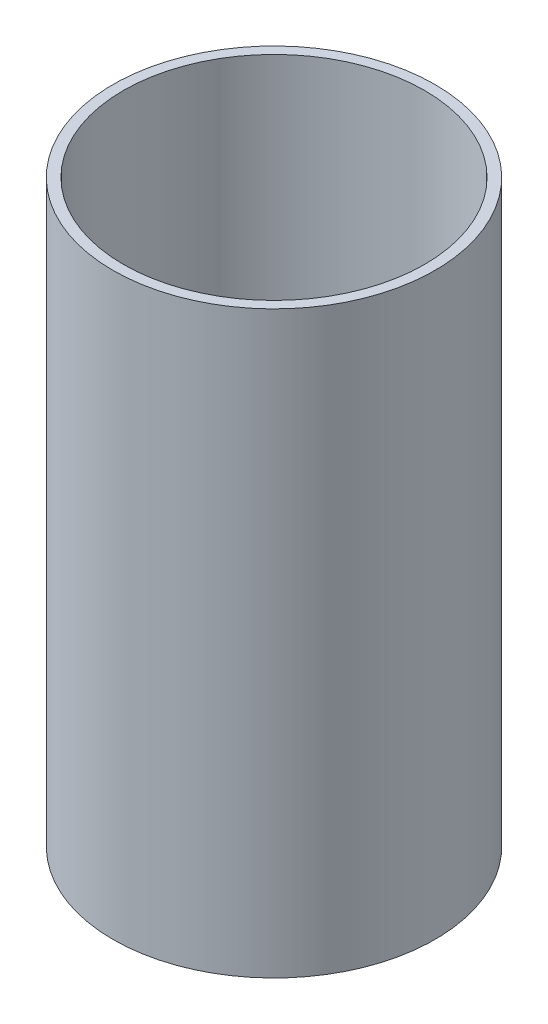
SolidWorks part; units mm, degrees
ref_plane "Front Plane" through (0, 0, 0) normal (0, 0, 1) x (1, 0, 0)
ref_plane "Top Plane" through (0, 0, 0) normal (0, 1, 0) x (1, 0, 0)
ref_plane "Right Plane" through (0, 0, 0) normal (1, 0, 0) x (0, 0, -1)
sketch "Sketch1" plane through (0, 0, 0) normal (0, 0, 1) x (1, 0, 0)
  line L0 (0, 0) -> (49.403, 0)
  line L1 (49.403, 0) -> (49.403, 177.8)
  line L2 (49.403, 177.8) -> (46.228, 177.8)
  line L3 (0, 0) -> (0, 3.175)
  line L4 (0, 3.175) -> (46.228, 3.175)
  line L5 (46.228, 3.175) -> (46.228, 177.8)
  dimension "D1" = 49.403
  dimension "D2" = 177.8
  dimension "D3" = 3.175
  dimension "D4" = 3.175
ref_axis "Central Axis" through (0, -8.89, 0) along (0, 1, 0)
revolve "Revolve1" add sketch "Sketch1" angle 360 about axis through (0, -8.89, 0) along (0, 1, 0)
